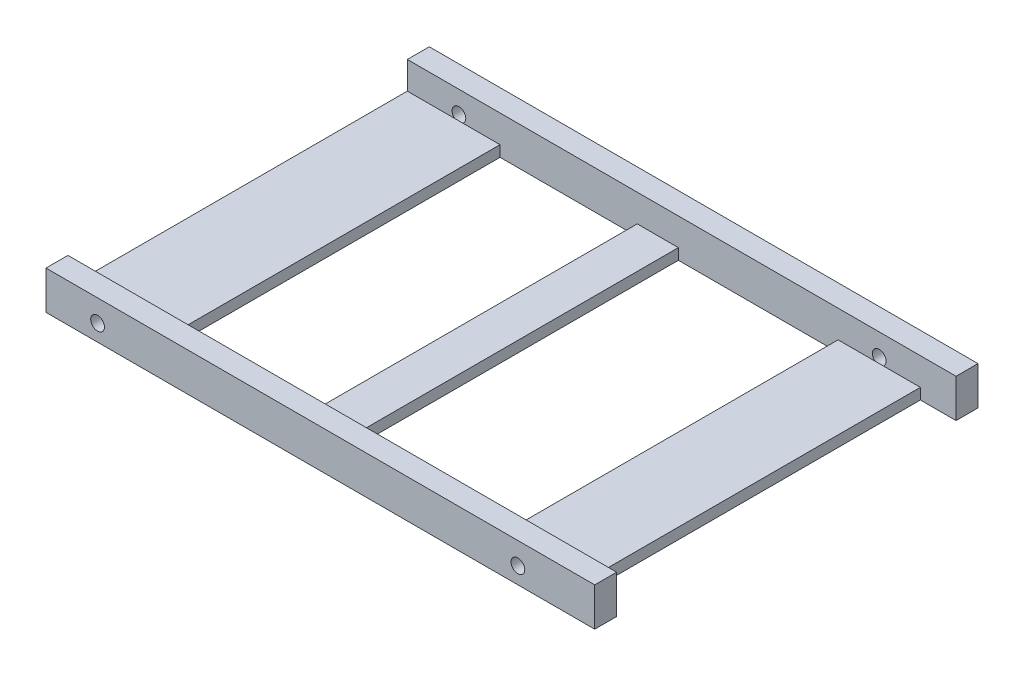
SolidWorks part; units mm, degrees
ref_plane "Front Plane" through (0, 0, 0) normal (0, 0, 1) x (1, 0, 0)
ref_plane "Top Plane" through (0, 0, 0) normal (0, 1, 0) x (1, 0, 0)
ref_plane "Right Plane" through (0, 0, 0) normal (1, 0, 0) x (0, 0, -1)
sketch "Sketch1" plane through (0, 0, 0) normal (0, 1, 0) x (1, 0, 0)
  line L1 (0, 0) -> (100, 0)
  line L2 (0, 0) -> (0, 69.85)
  line L3 (0, 69.85) -> (100, 69.85)
  line L4 (100, 0) -> (100, 69.85)
  dimension "D1" = 69.85
  dimension "D2" = 100
extrude "Boss-Extrude1" add sketch "Sketch1" along normal blind 7
sketch "Sketch2" plane through (0, 0, 0) normal (0, 0, 1) x (1, 0, 0)
  line L0 (0, 3) -> (100, 3) construction
  line L1 (0, 7) -> (0, 0) construction
  line L2 (100, 7) -> (100, 0) construction
  line L3 (0, 0) -> (100, 0) construction
  line L4 (9.4, 7) -> (9.4, 0) construction
  line L5 (0, 7) -> (100, 7) construction
  line L6 (86, 7) -> (86, 0) construction
  circle A1 centre (86, 3) radius 1.25
  circle A2 centre (9.4, 3) radius 1.25
  point P18 (0, 0)
  point P19 (0, 0)
  dimension "D4" = 2.5
  dimension "D1" = 3
  dimension "D2" = 90.6
  dimension "D3" = 14
extrude "Cut-Extrude1" cut sketch "Sketch2" against normal blind 4
sketch "Sketch3" plane through (0, 7, 0) normal (0, 1, 0) x (1, 0, 0)
  line L0 (100, 0) -> (100, 69.85) construction
  line L1 (16.9, 65.85) -> (41.9, 65.85)
  line L2 (16.9, 65.85) -> (16.9, 4)
  line L3 (16.9, 4) -> (41.9, 4)
  line L4 (41.9, 65.85) -> (41.9, 4)
  line L5 (49.4, 65.85) -> (78.5, 65.85)
  line L6 (49.4, 65.85) -> (49.4, 4)
  line L7 (49.4, 4) -> (78.5, 4)
  line L8 (78.5, 65.85) -> (78.5, 4)
  line L9 (100, 65.85) -> (93.5, 65.85)
  line L10 (100, 65.85) -> (100, 4)
  line L11 (100, 4) -> (93.5, 4)
  line L12 (93.5, 65.85) -> (93.5, 4)
  line L13 (100, 69.85) -> (0, 69.85) construction
  line L14 (0, 0) -> (100, 0) construction
  dimension "D1" = 4
  dimension "D2" = 4
  dimension "D3" = 6.5
  dimension "D4" = 21.5
  dimension "D5" = 83.1
  dimension "D6" = 25
  dimension "D7" = 7.5
extrude "Cut-Extrude2" cut sketch "Sketch3" against normal through all
sketch "Sketch4" plane through (93.5, 0, 0) normal (1, 0, 0) x (0, 0, -1)
  line L5 (4, 0) -> (4, 7) construction
  line L6 (65.85, 7) -> (4, 7)
  line L7 (65.85, 7) -> (65.85, 2)
  line L8 (65.85, 2) -> (4, 2)
  line L9 (4, 7) -> (4, 2)
  dimension "D1" = 5
extrude "Cut-Extrude3" cut sketch "Sketch4" against normal through all
ref_plane "Plane1" through (0, 0, -34.925) normal (0, 0, 1) x (1, 0, 0)
mirror "Mirror1" about plane through (0, 0, -34.925) normal (0, 0, 1) of "Cut-Extrude1"
equation "\"D2@Sketch3\"=\"D1@Sketch3\""
